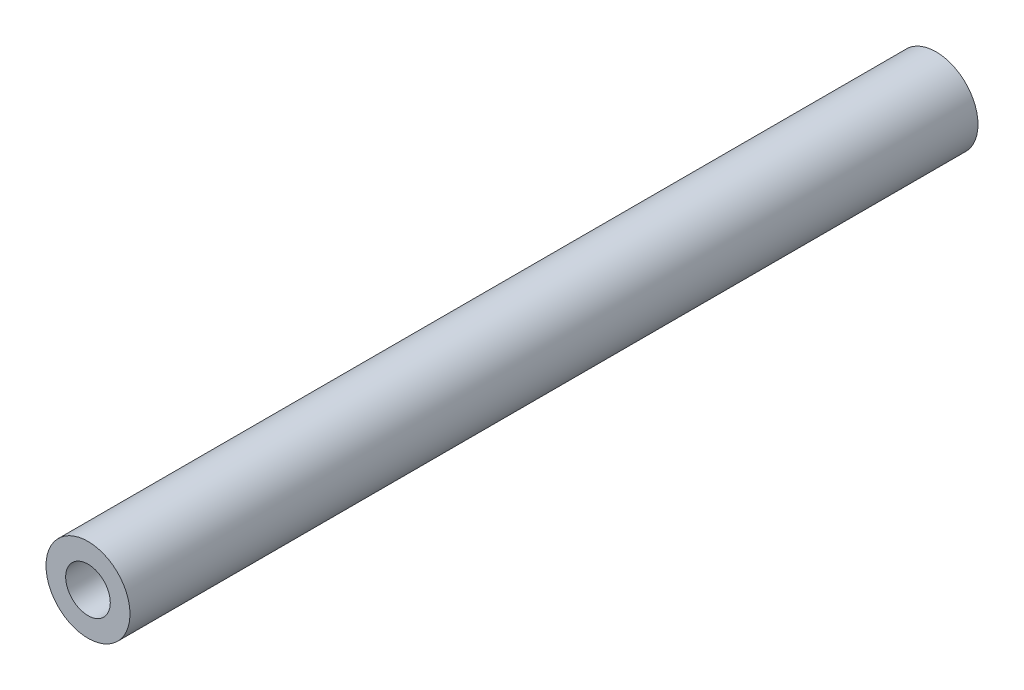
SolidWorks part; units mm, degrees
material "AISI 1020"
ref_plane "Спереди" through (0, 0, 0) normal (0, 0, 1) x (1, 0, 0)
ref_plane "Сверху" through (0, 0, 0) normal (0, 1, 0) x (1, 0, 0)
ref_plane "Справа" through (0, 0, 0) normal (1, 0, 0) x (0, 0, -1)
sketch "Эскиз1" plane through (0, 0, 0) normal (0, 0, 1) x (1, 0, 0)
  circle A0 centre (100, -317) radius 8
  dimension "D1" = 16
extrude "Бобышка-Вытянуть1" add sketch "Эскиз1" along normal up to surface (161.6 mm away)
ref_point "Точка1"
ref_point "Точка2"
hole_wizard "Отверстие обработанное метчиком M103" positions "Эскиз6" profile "Эскиз7" tap size "M10" standard "ISO"
sketch "Эскиз6" plane through (0, 0, 161.6) normal (0, 0, 1) x (1, 0, 0)
  point P0 (100, -317)
sketch "Эскиз7" plane through (100, -317, 161.6) normal (1, 0, 0) x (0, -1, 0)
  line L0 (0, 0) -> (0, 37.5537)
  line L1 (0, 37.5537) -> (4.25, 35)
  line L2 (4.25, 35) -> (4.25, 0)
  line L5 (4.25, 0) -> (0, 0)
  line L10 (0, 37.5537) -> (-4.25, 35) construction
  line L11 (0, -6.35) -> (0, 107.95) construction
  dimension "Диаметр сверла" = 8.5
  dimension "Глубина сверла" = 35
  dimension "Угол заточки сверла" = 118
cosmetic thread "Отверстие резьбы3" parameters "D1"=25, "D2"=10
hole_wizard "Отверстие обработанное метчиком M104" positions "Эскиз8" profile "Эскиз9" tap size "M10" standard "ISO"
sketch "Эскиз8" plane through (0, 0, 0) normal (0, 0, -1) x (-1, 0, 0)
  point P0 (-100, -317)
sketch "Эскиз9" plane through (100, -317, 0) normal (1, 0, 0) x (0, 1, 0)
  line L0 (0, 0) -> (0, 37.5537)
  line L1 (0, 37.5537) -> (4.25, 35)
  line L2 (4.25, 35) -> (4.25, 0)
  line L5 (4.25, 0) -> (0, 0)
  line L10 (0, 37.5537) -> (-4.25, 35) construction
  line L11 (0, -6.35) -> (0, 107.95) construction
  dimension "Диаметр сверла" = 8.5
  dimension "Глубина сверла" = 35
  dimension "Угол заточки сверла" = 118
cosmetic thread "Отверстие резьбы4" parameters "D1"=25, "D2"=10
